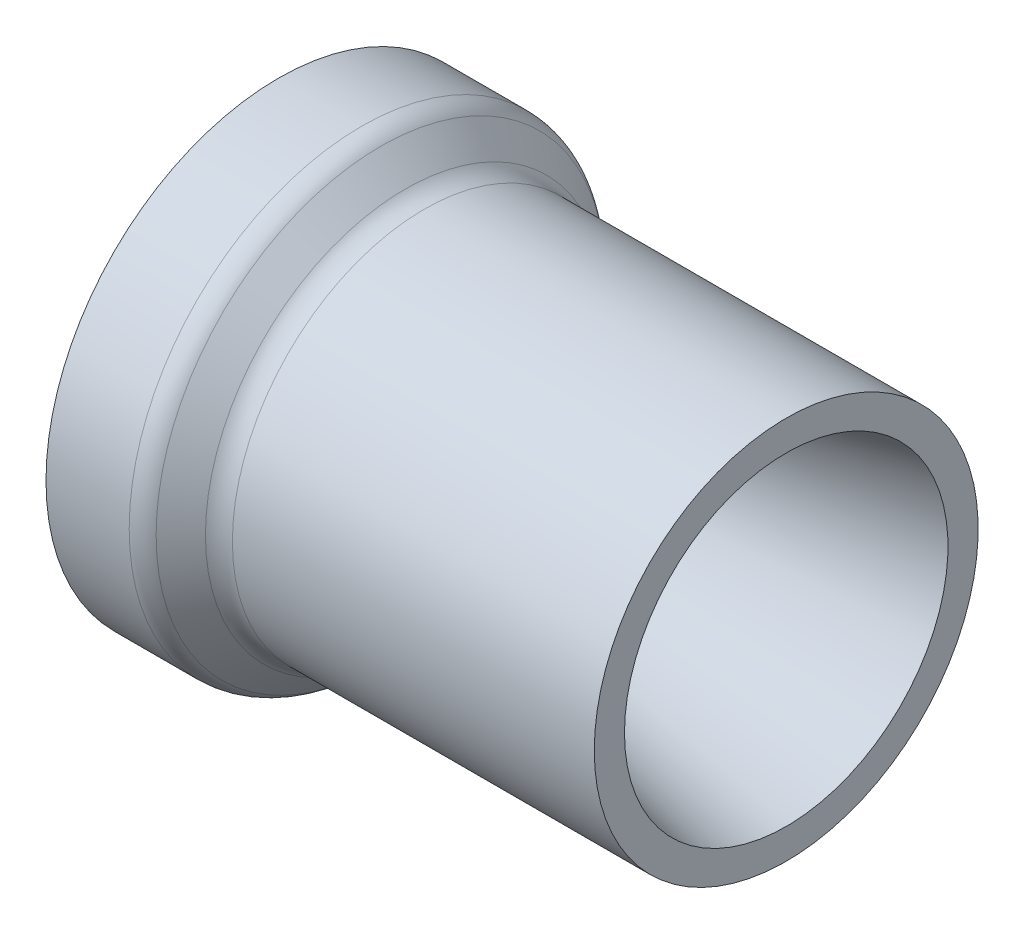
SolidWorks part; units mm, degrees
material "C (Graphite)"
ref_plane "Front Plane" through (0, 0, 0) normal (0, 0, 1) x (1, 0, 0)
ref_plane "Top Plane" through (0, 0, 0) normal (0, 1, 0) x (1, 0, 0)
ref_plane "Right Plane" through (0, 0, 0) normal (1, 0, 0) x (0, 0, -1)
sketch "Sketch1" plane through (0, 0, 0) normal (0, 0, 1) x (1, 0, 0)
  line L0 (0, 0.2921) -> (19.5947, 0.2921)
  line L1 (119.619, 16.9291) -> (24.021, 37.2491)
  line L2 (0, 0.2921) -> (0, 6.6421)
  line L3 (0, 55.0291) -> (76.2, 55.0291) construction
  line L5 (17.671, 37.2491) -> (24.021, 37.2491)
  line L14 (0, 6.6421) -> (17.671, 37.2491)
  line L15 (24.0849, 2.152) -> (29.8901, 7.9572)
  line L16 (34.3803, 9.8171) -> (119.619, 9.8171)
  line L17 (119.619, 9.8171) -> (119.619, 16.9291)
  arc A2 (19.5947, 0.2921) -> (24.0849, 2.152) centre (19.5947, 6.6421) ccw
  arc A3 (29.8901, 7.9572) -> (34.3803, 9.8171) centre (34.3803, 3.4671) cw
  point P13 (22.225, 0.2921)
  point P16 (31.75, 9.8171)
  dimension "D13" = 6.35
  dimension "D11" = 6.35
  dimension "D2" = 54.737
  dimension "D3" = 6.35
  dimension "D4" = 60
  dimension "D5" = 22.225
  dimension "D6" = 9.525
  dimension "D7" = 12
  dimension "D8" = 135
  dimension "D9" = 17.78
  dimension "D10" = 6.35
  dimension "D12" = 38.1
revolve "Revolve1" add sketch "Sketch1" angle 360 about L3
